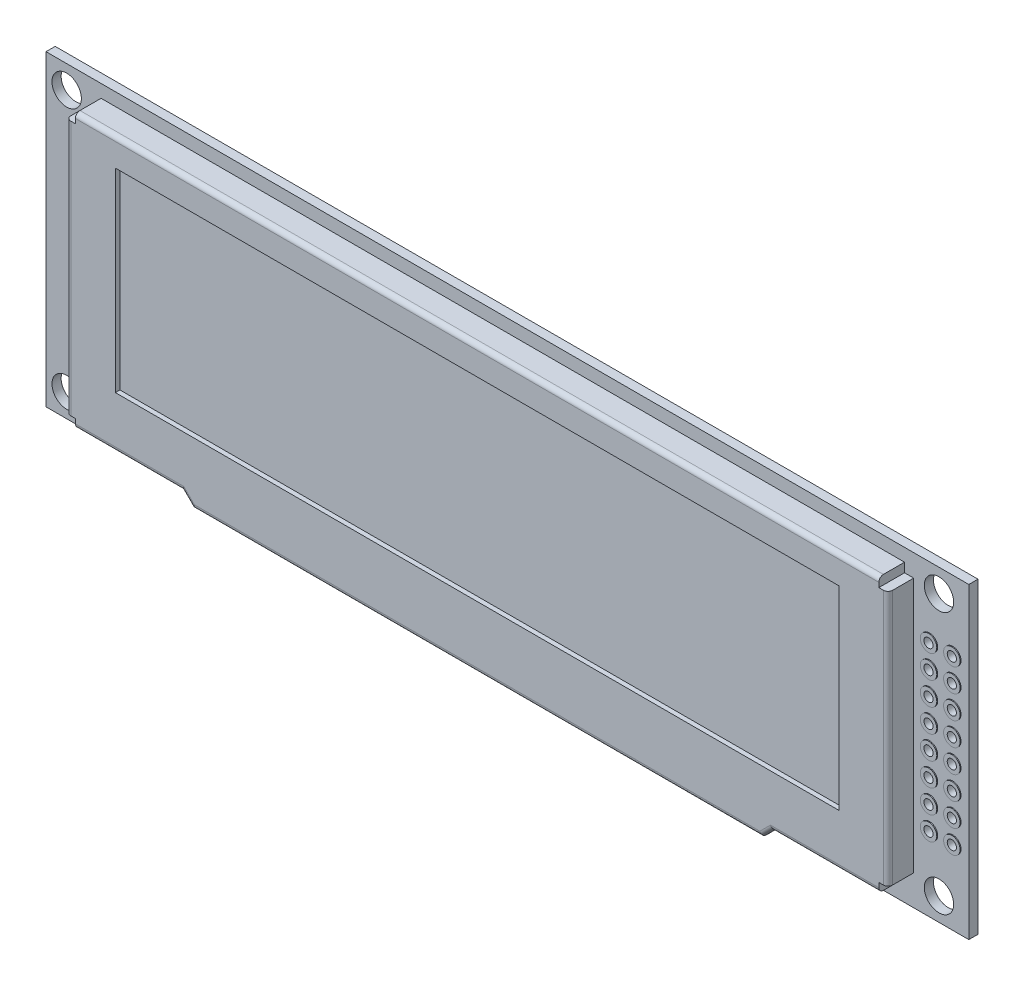
SolidWorks part; units mm, degrees
ref_plane "Спереди" through (0, 0, 0) normal (0, 0, 1) x (1, 0, 0)
ref_plane "Сверху" through (0, 0, 0) normal (0, 1, 0) x (1, 0, 0)
ref_plane "Справа" through (0, 0, 0) normal (1, 0, 0) x (0, 0, -1)
sketch "Эскиз1" plane through (0, 0, 0) normal (0, 0, 1) x (1, 0, 0)
  line L0 (-50.25, 0) -> (50.25, 0) construction
  line L1 (-50.25, 16.75) -> (50.25, 16.75)
  line L2 (-50.25, 16.75) -> (-50.25, -16.75)
  line L3 (-50.25, -16.75) -> (50.25, -16.75)
  line L4 (50.25, 16.75) -> (50.25, -16.75)
  line L5 (-50.25, 16.75) -> (50.25, -16.75) construction
  line L6 (-50.25, -16.75) -> (50.25, 16.75) construction
  circle A0 centre (-48, 14.25) radius 1.6
  circle A1 centre (47, 14.25) radius 1.6
  circle A2 centre (47, -14.25) radius 1.6
  circle A3 centre (-48, -14.25) radius 1.6
  point P0 (0, 0)
  dimension "D4" = 3.2
  dimension "D1" = 100.5
  dimension "D2" = 33.5
  dimension "D3" = 95
  dimension "D5" = 3.25
  dimension "D6" = 28.5
extrude "Бобышка-Вытянуть1" add sketch "Эскиз1" along normal blind 1
sketch "Эскиз2" plane through (0, 0, 1) normal (0, 0, 1) x (1, 0, 0)
  line L0 (-0.5, 16.75) -> (-0.5, -16.75) construction
  line L1 (50.25, 16.75) -> (-50.25, 16.75) construction
  line L3 (43.25, 15.35) -> (-44.25, 15.35)
  line L4 (-44.25, 15.35) -> (-44.25, 14.35)
  line L5 (-44.25, 14.35) -> (-45.25, 14.35)
  line L6 (-45.25, 14.35) -> (-45.25, -13.45)
  line L7 (-45.25, -13.45) -> (-44.25, -13.45)
  line L8 (-44.25, -13.45) -> (-44.25, -14.45)
  line L9 (-44.25, -14.45) -> (-32.65, -14.45)
  line L10 (-32.65, -14.45) -> (-31.5, -15.6)
  line L11 (-31.5, -15.6) -> (30.5, -15.6)
  line L12 (31.65, -14.45) -> (30.5, -15.6)
  line L13 (43.25, -14.45) -> (31.65, -14.45)
  line L14 (43.25, -13.45) -> (43.25, -14.45)
  line L15 (44.25, -13.45) -> (43.25, -13.45)
  line L16 (44.25, 14.35) -> (44.25, -13.45)
  line L17 (43.25, 14.35) -> (44.25, 14.35)
  line L18 (43.25, 15.35) -> (43.25, 14.35)
  line L19 (50.25, -16.75) -> (50.25, 16.75) construction
  point P18 (-0.5, -15.6)
  point P25 (-0.5, 15.35)
  dimension "D1" = 89.5
  dimension "D2" = 64.3
  dimension "D3" = 62
  dimension "D4" = 29.8
  dimension "D5" = 45
  dimension "D6" = 1.4
  dimension "D7" = 1
  dimension "D8" = 6
  dimension "D9" = 6
extrude "Бобышка-Вытянуть2" add sketch "Эскиз2" along normal blind 2.8
fillet "Скругление1" radius 0.5 8 edges at (-0.5, 15.35, 3.8) (44.25, 0.45, 3.8) (37.45, -14.45, 3.8) (31.075, -15.025, 3.8) (-45.25, 0.45, 3.8) (-0.5, -15.6, 3.8) (-32.075, -15.025, 3.8) (-38.45, -14.45, 3.8)
sketch "Эскиз3" plane through (0, 0, 3.8) normal (0, 0, 1) x (1, 0, 0)
  line L0 (50.25, -16.75) -> (50.25, 16.75) construction
  line L1 (-39.9, 12.35) -> (38.9, 12.35)
  line L2 (-39.9, 12.35) -> (-39.9, -8.83)
  line L3 (-39.9, -8.83) -> (38.9, -8.83)
  line L4 (38.9, 12.35) -> (38.9, -8.83)
  line L5 (-39.9, 12.35) -> (38.9, -8.83) construction
  line L6 (-39.9, -8.83) -> (38.9, 12.35) construction
  line L7 (50.25, 16.75) -> (-50.25, 16.75) construction
  point P0 (-0.5, 1.76)
  dimension "D1" = 78.8
  dimension "D2" = 21.18
  dimension "D3" = 11.35
  dimension "D4" = 4.4
extrude "Вырез-Вытянуть1" cut sketch "Эскиз3" against normal blind 0.5
sketch "Эскиз4" plane through (0, 0, 1) normal (0, 0, 1) x (1, 0, 0)
  line L0 (50.25, -16.75) -> (50.25, 16.75) construction
  line L1 (-50.25, -16.75) -> (50.25, -16.75) construction
  circle A0 centre (48.5, -8.64) radius 0.9
  circle A1 centre (45.96, -8.64) radius 0.9
  circle A2 centre (45.96, -6.1) radius 0.9
  circle A3 centre (45.96, -3.56) radius 0.9
  circle A4 centre (45.96, -1.02) radius 0.9
  circle A5 centre (45.96, 1.52) radius 0.9
  circle A6 centre (45.96, 4.06) radius 0.9
  circle A7 centre (45.96, 6.6) radius 0.9
  circle A8 centre (45.96, 9.14) radius 0.9
  circle A9 centre (48.5, -6.1) radius 0.9
  circle A10 centre (48.5, -3.56) radius 0.9
  circle A11 centre (48.5, -1.02) radius 0.9
  circle A12 centre (48.5, 1.52) radius 0.9
  circle A13 centre (48.5, 4.06) radius 0.9
  circle A14 centre (48.5, 6.6) radius 0.9
  circle A15 centre (48.5, 9.14) radius 0.9
  dimension "D3" = 1.8
  dimension "D1" = 1.75
  dimension "D2" = 8.11
  dimension "D4" = 2
  dimension "D5" = 8
extrude "Бобышка-Вытянуть3" add sketch "Эскиз4" along normal blind 0.1
sketch "Эскиз5" plane through (0, 0, 1.1) normal (0, 0, 1) x (1, 0, 0)
  circle A0 centre (48.5, -8.64) radius 0.5
  circle A1 centre (45.96, -8.64) radius 0.5
  circle A2 centre (45.96, -6.1) radius 0.5
  circle A3 centre (45.96, -3.56) radius 0.5
  circle A4 centre (45.96, -1.02) radius 0.5
  circle A5 centre (45.96, 1.52) radius 0.5
  circle A6 centre (45.96, 4.06) radius 0.5
  circle A7 centre (45.96, 6.6) radius 0.5
  circle A8 centre (45.96, 9.14) radius 0.5
  circle A9 centre (48.5, -6.1) radius 0.5
  circle A10 centre (48.5, -3.56) radius 0.5
  circle A11 centre (48.5, -1.02) radius 0.5
  circle A12 centre (48.5, 1.52) radius 0.5
  circle A13 centre (48.5, 4.06) radius 0.5
  circle A14 centre (48.5, 6.6) radius 0.5
  circle A15 centre (48.5, 9.14) radius 0.5
  dimension "D1" = 1
  dimension "D2" = 2
  dimension "D3" = 8
extrude "Вырез-Вытянуть2" cut sketch "Эскиз5" against normal through all
